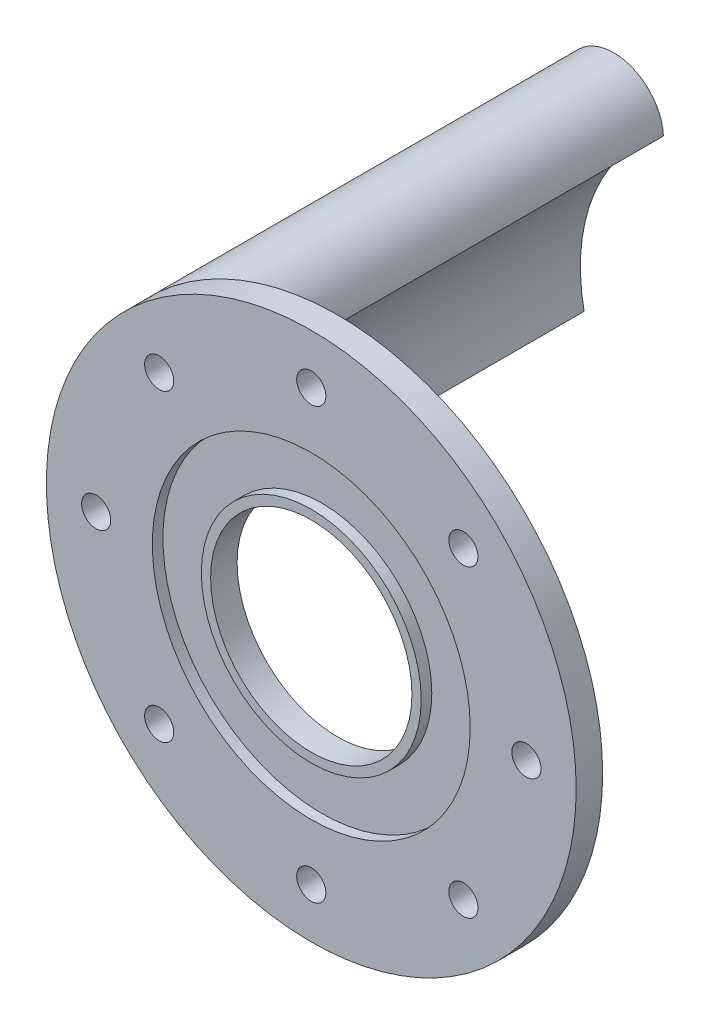
SolidWorks part; units mm, degrees
ref_plane "Alzado" through (0, 0, 0) normal (0, 0, 1) x (1, 0, 0)
ref_plane "Planta" through (0, 0, 0) normal (0, 1, 0) x (1, 0, 0)
ref_plane "Vista lateral" through (0, 0, 0) normal (1, 0, 0) x (0, 0, -1)
sketch "Croquis1" plane through (0, 0, 0) normal (0, 0, 1) x (1, 0, 0)
  circle A0 centre (0, 0) radius 50
  circle A1 centre (0, 0) radius 19
  dimension "D1" = 100
  dimension "D2" = 38
extrude "Saliente-Extruir1" add sketch "Croquis1" along normal blind 5
sketch "Croquis4" plane through (0, 0, 5) normal (0, 0, 1) x (1, 0, 0)
  circle A0 centre (0, 0) radius 20.75
  circle A1 centre (0, 0) radius 30
  dimension "D1" = 41.5
  dimension "D2" = 60
extrude "Cortar-Extruir1" cut sketch "Croquis4" against normal blind 2
sketch "Croquis5" plane through (0, 0, 5) normal (0, 0, 1) x (1, 0, 0)
  circle A0 centre (0, 0) radius 40.603
  circle A1 centre (40.603, 0) radius 2.75
  circle A2 centre (28.7107, -28.7107) radius 2.75
  circle A3 centre (0, -40.603) radius 2.75
  circle A4 centre (-28.7107, -28.7107) radius 2.75
  circle A5 centre (-40.603, 0) radius 2.75
  circle A6 centre (-28.7107, 28.7107) radius 2.75
  circle A7 centre (0, 40.603) radius 2.75
  circle A8 centre (28.7107, 28.7107) radius 2.75
  point P21 (0, 0)
  dimension "D2" = 5.5
  dimension "D1" = 8
extrude "Cortar-Extruir2" cut sketch "Croquis5" against normal up to surface (5 mm away) contours A1 | A8 | A7 | A6 | A5 | A4 | A3 | A2 up to face at (50, 0, 0)
sketch "Croquis8" plane through (0, 0, 0) normal (0, 0, -1) x (-1, 0, 0)
  circle A0 centre (28.7107, 28.7107) radius 3.5
  arc A1 (34.2992, -6.9689) -> (19.3254, 29.1809) centre (0, 0) ccw
  arc A2 (50, 0) -> (35.3553, 35.3553) centre (0, 0) ccw
  circle A3 centre (40.603, 0) radius 3.5
  arc A4 (34.2992, -6.9689) -> (50, 0) centre (40.603, 0) ccw
  arc A5 (35.3553, 35.3553) -> (19.3254, 29.1809) centre (28.7107, 28.7107) ccw
  dimension "D1" = 7
  dimension "D2" = 70
  dimension "D3" = 7
extrude "Saliente-Extruir2" add sketch "Croquis8" along normal blind 80.8 separate body
sketch "Croquis9" plane through (0, 0, 0) normal (0, 0, 1) x (1, 0, 0)
  line L1 (-40.603, 4.9075) -> (-44.853, 2.4537)
  line L2 (-44.853, 2.4537) -> (-44.853, -2.4537)
  line L3 (-44.853, -2.4537) -> (-40.603, -4.9075)
  line L4 (-40.603, -4.9075) -> (-36.353, -2.4537)
  line L5 (-36.353, -2.4537) -> (-36.353, 2.4537)
  line L6 (-36.353, 2.4537) -> (-40.603, 4.9075)
  line L7 (-23.9446, 27.541) -> (-25.3147, 32.2533)
  line L8 (-25.3147, 32.2533) -> (-30.0807, 33.423)
  line L9 (-30.0807, 33.423) -> (-33.4767, 29.8803)
  line L10 (-33.4767, 29.8803) -> (-32.1066, 25.168)
  line L11 (-32.1066, 25.168) -> (-27.3406, 23.9983)
  line L12 (-27.3406, 23.9983) -> (-23.9446, 27.541)
  circle A0 centre (-40.603, 0) radius 4.25 construction
  circle A1 centre (-28.7107, 28.7107) radius 4.25 construction
  dimension "D1" = 8.5
  dimension "D2" = 8.5
extrude "Cortar-Extruir3" cut sketch "Croquis9" against normal blind 11
sketch "Croquis10" plane through (0, 0, -80.8) normal (0, 0, -1) x (-1, 0, 0)
  line L1 (27.5311, 23.947) -> (32.2463, 25.3073)
  line L2 (32.2463, 25.3073) -> (33.4258, 30.071)
  line L3 (33.4258, 30.071) -> (29.8902, 33.4743)
  line L4 (29.8902, 33.4743) -> (25.175, 32.114)
  line L5 (25.175, 32.114) -> (23.9955, 27.3503)
  line L6 (23.9955, 27.3503) -> (27.5311, 23.947)
  line L7 (40.603, -4.9075) -> (44.853, -2.4537)
  line L8 (44.853, -2.4537) -> (44.853, 2.4537)
  line L9 (44.853, 2.4537) -> (40.603, 4.9075)
  line L10 (40.603, 4.9075) -> (36.353, 2.4537)
  line L11 (36.353, 2.4537) -> (36.353, -2.4537)
  line L12 (36.353, -2.4537) -> (40.603, -4.9075)
  circle A0 centre (28.7107, 28.7107) radius 4.25 construction
  circle A1 centre (40.603, 0) radius 4.25 construction
  dimension "D1" = 8.5
  dimension "D2" = 8.5
extrude "Cortar-Extruir4" cut sketch "Croquis10" against normal blind 19
sketch "Croquis13" plane through (0, 0, 0) normal (0, 0, 1) x (1, 0, 0)
  line L1 (-40.603, -2.9075) -> (-36.353, -0.4537)
  line L2 (-36.353, -0.4537) -> (-36.353, 4.4537)
  line L3 (-36.353, 4.4537) -> (-40.603, 6.9075)
  line L4 (-40.603, 6.9075) -> (-44.853, 4.4537)
  line L5 (-44.853, 4.4537) -> (-44.853, -0.4537)
  line L6 (-44.853, -0.4537) -> (-40.603, -2.9075)
  line L7 (-33.5335, 23.79) -> (-28.7301, 22.7844)
  line L8 (-28.7301, 22.7844) -> (-25.4575, 26.4414)
  line L9 (-25.4575, 26.4414) -> (-26.9883, 31.104)
  line L10 (-26.9883, 31.104) -> (-31.7916, 32.1096)
  line L11 (-31.7916, 32.1096) -> (-35.0642, 28.4527)
  line L12 (-35.0642, 28.4527) -> (-33.5335, 23.79)
  circle A0 centre (-40.603, 2) radius 4.25 construction
  circle A1 centre (-30.2609, 27.447) radius 4.25 construction
  arc A2 (-36.353, 4.4537) -> (-28.7301, 22.7844) centre (8.9557, -3.6378) cw
  arc A3 (-44.853, 4.4537) -> (-35.0642, 28.4527) centre (-3.4395, 1.5576) cw
  arc A4 (-50, 0) -> (-34.2992, -6.9689) centre (-40.603, 0) ccw
  arc A5 (-19.3254, 29.1809) -> (-34.2992, -6.9689) centre (0, 0) ccw
  arc A6 (-19.3254, 29.1809) -> (-35.3553, 35.3553) centre (-28.7107, 28.7107) ccw
  arc A7 (-35.3553, 35.3553) -> (-50, 0) centre (0, 0) ccw
  arc A8 (-50, 0) -> (-34.2992, -6.9689) centre (-40.603, 0) ccw
  arc A9 (-19.3254, 29.1809) -> (-34.2992, -6.9689) centre (0, 0) ccw
  arc A10 (-19.3254, 29.1809) -> (-35.3553, 35.3553) centre (-28.7107, 28.7107) ccw
  arc A11 (-35.3553, 35.3553) -> (-50, 0) centre (0, 0) ccw
  dimension "D2" = 8.5
  dimension "D3" = 2
  dimension "D4" = 2
  dimension "D5" = 8.5
  dimension "D1" = 0
extrude "Cortar-Extruir5" cut sketch "Croquis13" against normal up to surface (80.8 mm away) contours A3 L4 L3 A2 L7 L12 up to face at (-40.603, 0, -80.8)
